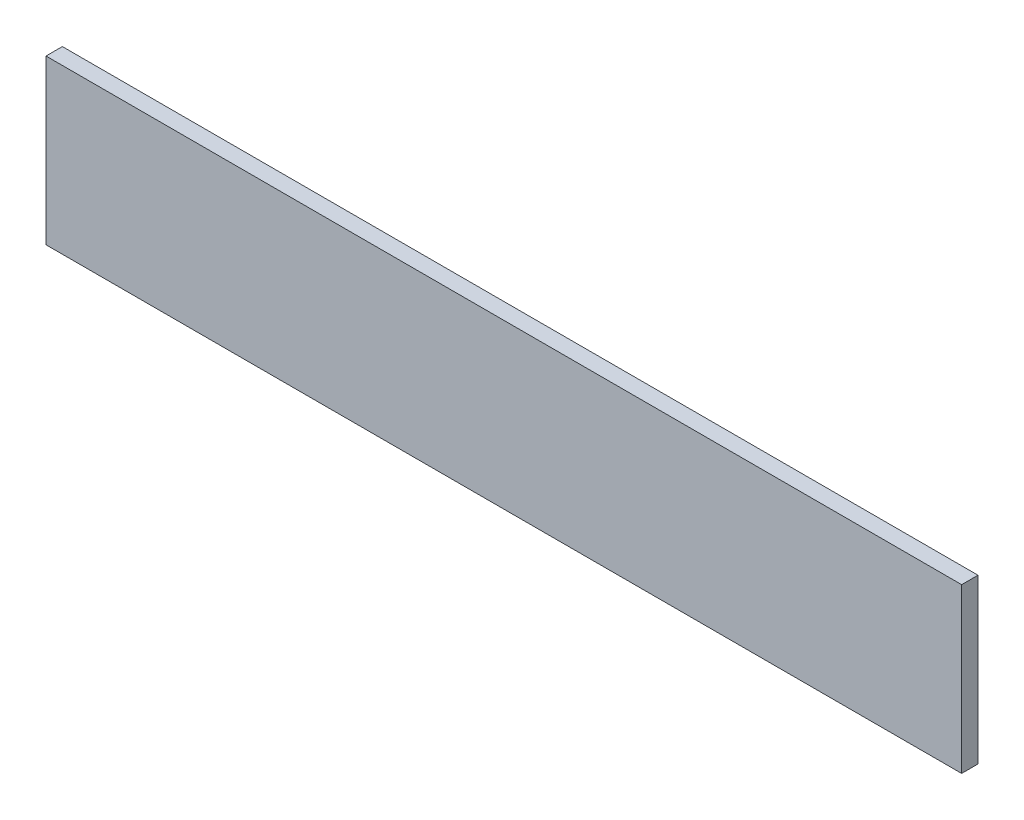
SolidWorks part; units mm, degrees
ref_plane "前视基准面" through (0, 0, 0) normal (0, 0, 1) x (1, 0, 0)
ref_plane "上视基准面" through (0, 0, 0) normal (0, 1, 0) x (1, 0, 0)
ref_plane "右视基准面" through (0, 0, 0) normal (1, 0, 0) x (0, 0, -1)
sketch "草图1" plane through (0, 0, 0) normal (0, 0, 1) x (1, 0, 0)
  line L1 (-140, -25) -> (140, -25)
  line L2 (-140, -25) -> (-140, 25)
  line L3 (-140, 25) -> (140, 25)
  line L4 (140, -25) -> (140, 25)
  line L5 (-140, -25) -> (140, 25) construction
  line L6 (-140, 25) -> (140, -25) construction
  point P0 (0, 0)
  dimension "D1" = 280
  dimension "D2" = 50
extrude "凸台-拉伸1" add sketch "草图1" along normal blind 5
